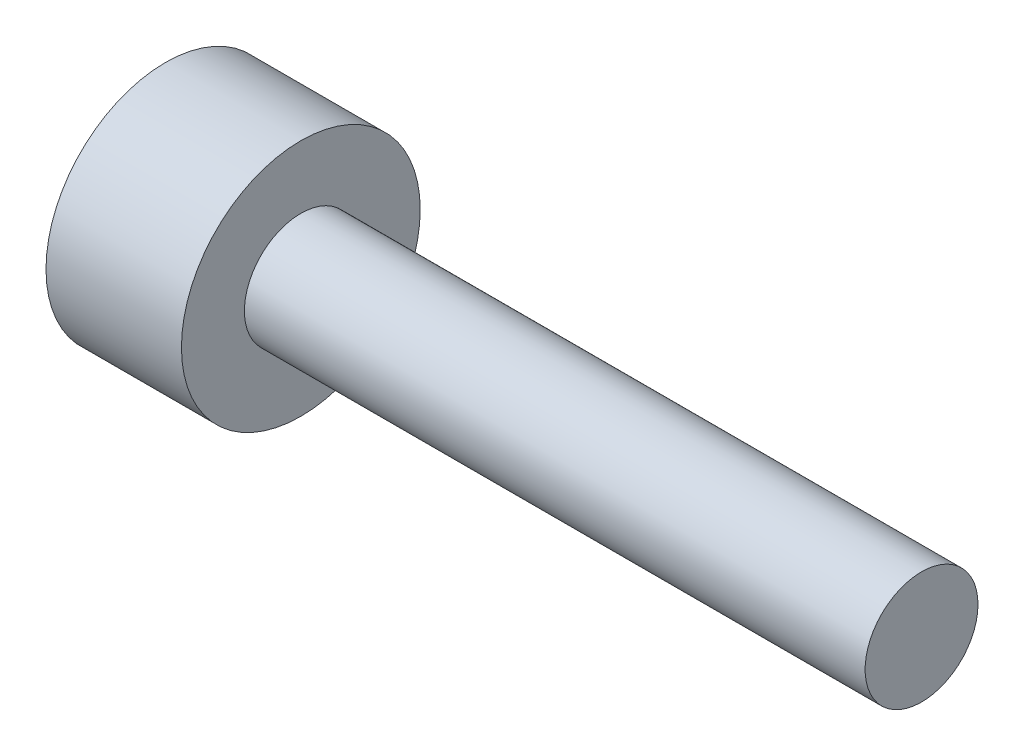
SolidWorks part; units mm, degrees
ref_plane "Front Plane" through (0, 0, 0) normal (0, 0, 1) x (1, 0, 0)
ref_plane "Top Plane" through (0, 0, 0) normal (0, 1, 0) x (1, 0, 0)
ref_plane "Right Plane" through (0, 0, 0) normal (1, 0, 0) x (0, 0, -1)
sketch "Sketch1" plane through (0, 0, 0) normal (1, 0, 0) x (0, 0, -1)
  circle A0 centre (0, 0) radius 0.125
  dimension "D1" = 0.25
extrude "Boss-Extrude1" add sketch "Sketch1" along normal blind 1.375
sketch "Sketch2" plane through (0, 0, 0) normal (-1, 0, 0) x (0, 0, 1)
  circle A0 centre (0, 0) radius 0.2645
  dimension "D1" = 0.5289
extrude "Boss-Extrude2" add sketch "Sketch2" along normal blind 0.3
sketch "Sketch3" plane through (-0.3, 0, 0) normal (-1, 0, 0) x (0, 0, 1)
  line L1 (0, 0.2078) -> (-0.18, 0.1039)
  line L2 (-0.18, 0.1039) -> (-0.18, -0.1039)
  line L3 (-0.18, -0.1039) -> (0, -0.2078)
  line L4 (0, -0.2078) -> (0.18, -0.1039)
  line L5 (0.18, -0.1039) -> (0.18, 0.1039)
  line L6 (0.18, 0.1039) -> (0, 0.2078)
  circle A0 centre (0, 0) radius 0.18 construction
  circle A1 centre (0, 0) radius 0.2645 construction
  dimension "D1" = 0.36
extrude "Cut-Extrude1" cut sketch "Sketch3" against normal blind 0.2
sketch "Sketch4" plane through (-0.1, 0, 0) normal (-1, 0, 0) x (0, 0, 1)
  circle A0 centre (0, 0) radius 0.18
  dimension "D1" = 0.36
extrude "Cut-Extrude2" cut sketch "Sketch4" against normal blind 0.1 draft 60
